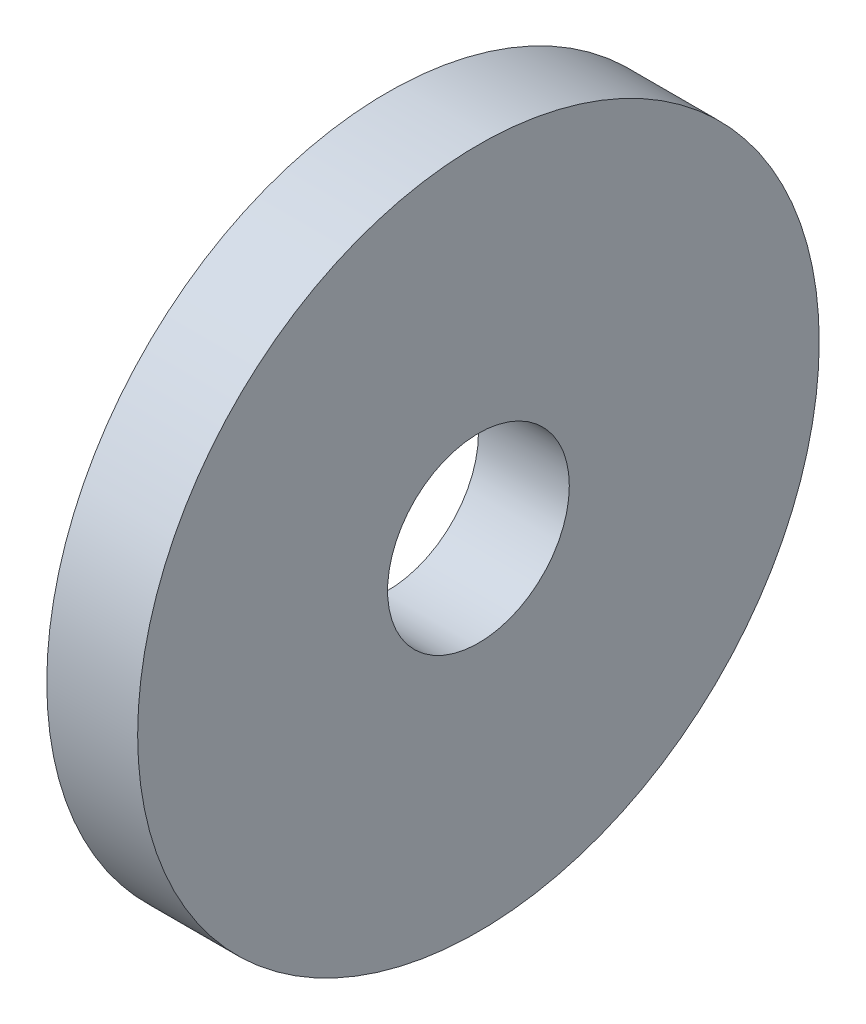
SolidWorks part; units mm, degrees
material "AISI 4130 Steel, normalized at 870C"
ref_plane "Front Plane" through (0, 0, 0) normal (0, 0, 1) x (1, 0, 0)
ref_plane "Top Plane" through (0, 0, 0) normal (0, 1, 0) x (1, 0, 0)
ref_plane "Right Plane" through (0, 0, 0) normal (1, 0, 0) x (0, 0, -1)
sketch "Sketch1" plane through (0, 0, 0) normal (1, 0, 0) x (0, 0, -1)
  circle A0 centre (0, 0) radius 37.5
  dimension "D1" = 75
extrude "Boss-Extrude1" add sketch "Sketch1" along normal blind 10
sketch "Sketch2" plane through (10, 0, 0) normal (1, 0, 0) x (0, 0, -1)
  circle A0 centre (0, 0) radius 10
  dimension "D1" = 20
extrude "Cut-Extrude1" cut sketch "Sketch2" against normal through all
